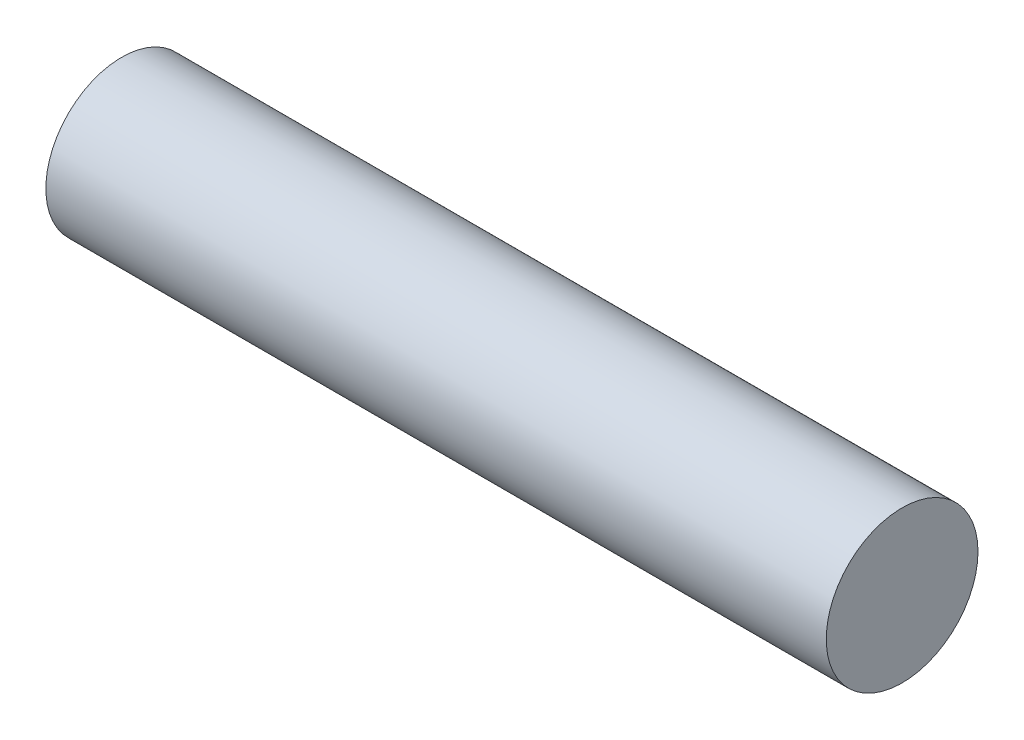
SolidWorks part; units mm, degrees
ref_plane "Спереди" through (0, 0, 0) normal (0, 0, 1) x (1, 0, 0)
ref_plane "Сверху" through (0, 0, 0) normal (0, 1, 0) x (1, 0, 0)
ref_plane "Справа" through (0, 0, 0) normal (1, 0, 0) x (0, 0, -1)
sketch "Эскиз1" plane through (0, 0, 0) normal (1, 0, 0) x (0, 0, -1)
  circle A0 centre (0, 0) radius 0.875
  dimension "D1" = 1.75
extrude "Бобышка-Вытянуть1" add sketch "Эскиз1" along normal blind 9
